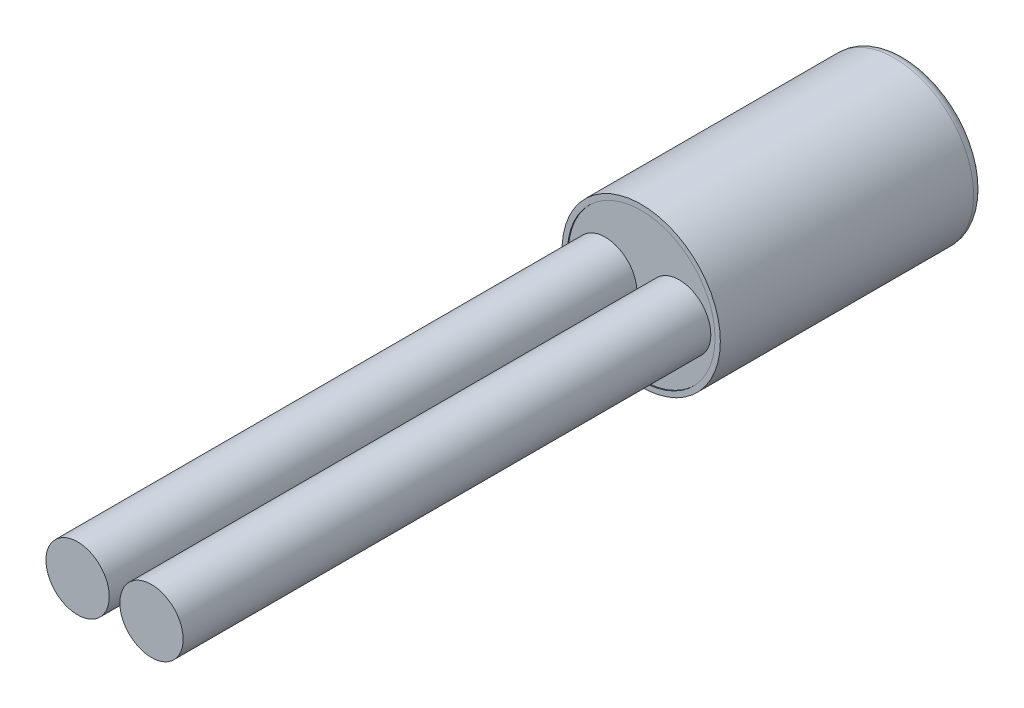
SolidWorks part; units mm, degrees
ref_plane "Plan de face" through (0, 0, 0) normal (0, 0, 1) x (1, 0, 0)
ref_plane "Plan de dessus" through (0, 0, 0) normal (0, 1, 0) x (1, 0, 0)
ref_plane "Plan de droite" through (0, 0, 0) normal (1, 0, 0) x (0, 0, -1)
sketch "Esquisse1" plane through (0, 0, 0) normal (0, 0, 1) x (1, 0, 0)
  circle A0 centre (0, 0) radius 1.5
extrude "Boss.-Extru.1" add sketch "Esquisse1" along normal blind 5
fillet "Congé1" radius 0.2 1 edges at (1.5, 0, 0)
sketch "Esquisse2" plane through (0, 0, 5) normal (0, 0, 1) x (1, 0, 0)
  circle A0 centre (0, 0) radius 1.4
extrude "Enlèv. mat.-Extru.1" cut sketch "Esquisse2" against normal blind 0.02
sketch "Esquisse3" plane through (0, 0, 4.98) normal (0, 0, 1) x (1, 0, 0)
  line L0 (0, 0) -> (1.4, 0) construction
  line L1 (1.4, 0) -> (0, 0) construction
  line L2 (0, 0) -> (-1.4, 0) construction
  line L3 (-1.4, 0) -> (-0.7, 0) construction
  line L4 (-0.7, 0) -> (0, 0) construction
  line L5 (0, 0) -> (0.7, 0) construction
  circle A0 centre (0, 0) radius 1.4 construction
  circle A1 centre (-0.7, 0) radius 0.6
  circle A2 centre (0.7, 0) radius 0.6
extrude "Boss.-Extru.2" add sketch "Esquisse3" along normal blind 10
